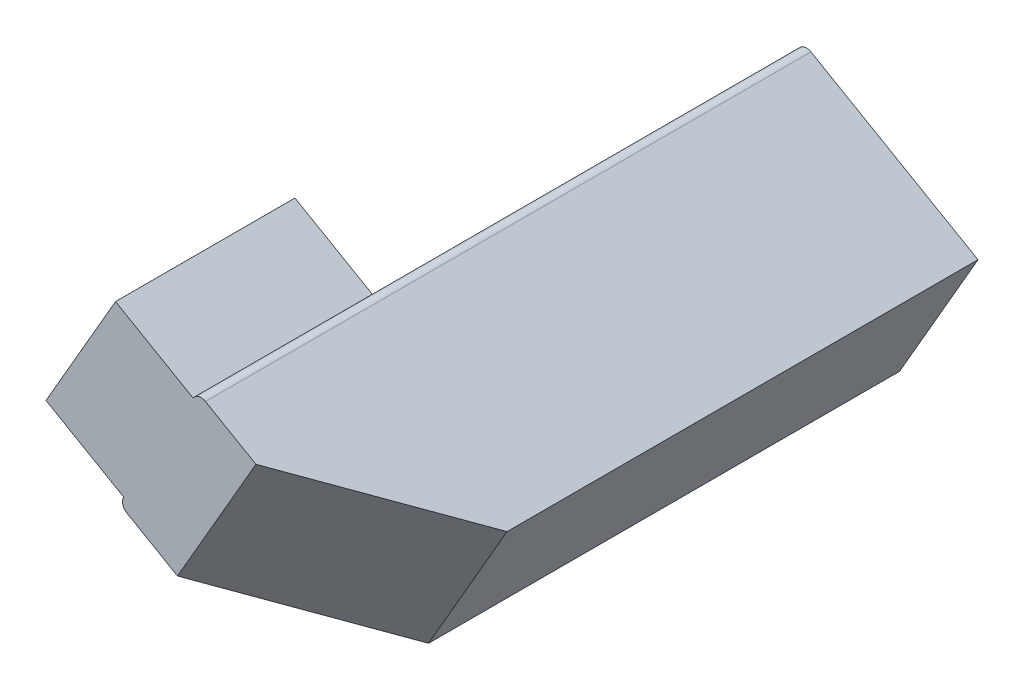
SolidWorks part; units mm, degrees
material "6061 Alloy"
ref_plane "Front Plane" through (0, 0, 0) normal (0, 0, 1) x (1, 0, 0)
ref_plane "Top Plane" through (0, 0, 0) normal (0, 1, 0) x (1, 0, 0)
ref_plane "Right Plane" through (0, 0, 0) normal (1, 0, 0) x (0, 0, -1)
sketch "Sketch2" plane through (0, 0, 0) normal (0, 0, 1) x (1, 0, 0)
  line L12 (114.8381, -46.0946) -> (77.599, -24.5946)
  line L13 (74.867, -25.3266) -> (59.367, -52.1734)
  line L14 (60.099, -54.9054) -> (97.3381, -76.4054)
  line L15 (97.3381, -76.4054) -> (114.8381, -46.0946)
  arc A6 (77.599, -24.5946) -> (74.867, -25.3266) centre (76.599, -26.3266) ccw
  arc A7 (59.367, -52.1734) -> (60.099, -54.9054) centre (61.099, -53.1734) ccw
extrude "Boss-Extrude1" add sketch "Sketch2" along normal blind 135
sketch "Sketch3" plane through (67.117, -38.75, 0) normal (-0.866, 0.5, 0) x (0, 0, 1)
  line L0 (135, 15.5) -> (135, -15.5)
  line L1 (135, -15.5) -> (95, -15.5)
  line L2 (135, -15.5) -> (0, -15.5) construction
  line L3 (95, -15.5) -> (95, 15.5)
  line L4 (135, 15.5) -> (0, 15.5) construction
  line L5 (95, 15.5) -> (135, 15.5)
  dimension "D1" = 40
extrude "Boss-Extrude2" add sketch "Sketch3" along normal blind 20
chamfer "Chamfer1" distance 30 angle 45 1 edges at (106.0881, -61.25, 135)
